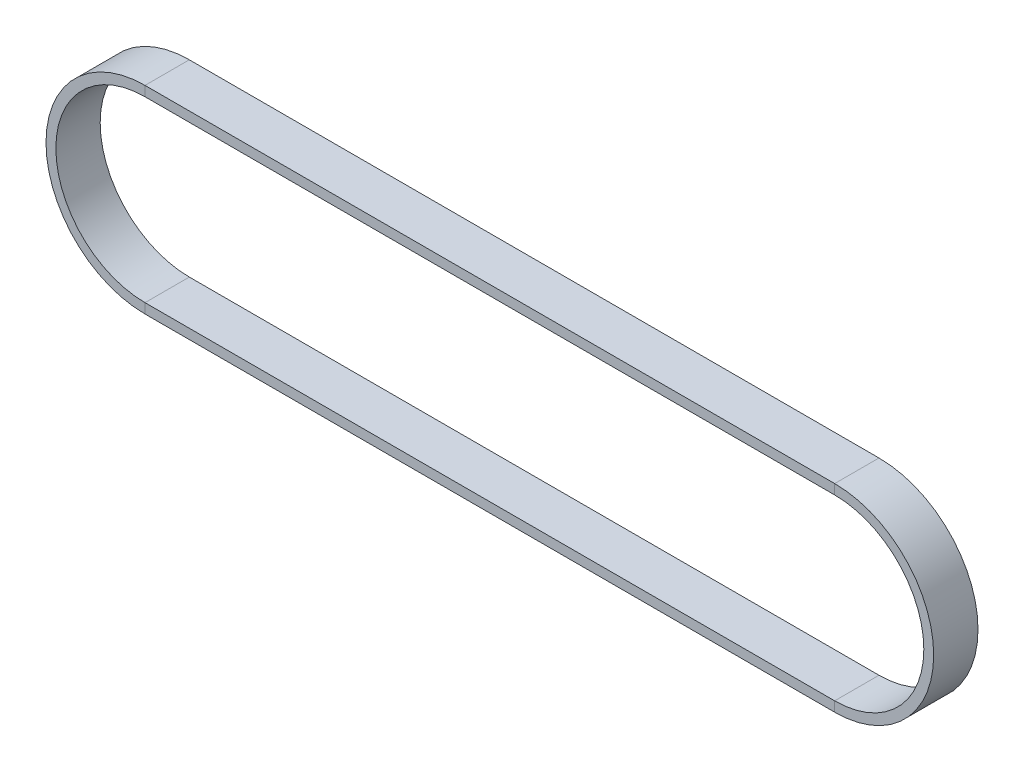
SolidWorks part; units mm, degrees
ref_plane "Front Plane" through (0, 0, 0) normal (0, 0, 1) x (1, 0, 0)
ref_plane "Top Plane" through (0, 0, 0) normal (0, 1, 0) x (1, 0, 0)
ref_plane "Right Plane" through (0, 0, 0) normal (1, 0, 0) x (0, 0, -1)
sketch "Sketch1" plane through (0, 0, 0) normal (0, 0, 1) x (1, 0, 0)
  line L0 (0, 19.1008) -> (140.0251, 19.1008)
  line L1 (0, -19.1008) -> (140.0251, -19.1008)
  arc A0 (0, 19.1008) -> (0, -19.1008) centre (0, 0) ccw
  arc A1 (140.0251, -19.1008) -> (140.0251, 19.1008) centre (140.0251, 0) ccw
  dimension "D1" = 38.2016
  dimension "D2" = 38.2016
  dimension "D3" = 140.0251
sketch "Sketch2" plane through (0, 0, 0) normal (1, 0, 0) x (0, 0, -1)
  line L1 (4.5, 18.1008) -> (-4.5, 18.1008)
  line L2 (4.5, 18.1008) -> (4.5, 20.1008)
  line L3 (4.5, 20.1008) -> (-4.5, 20.1008)
  line L4 (-4.5, 18.1008) -> (-4.5, 20.1008)
  line L5 (4.5, 18.1008) -> (-4.5, 20.1008) construction
  line L6 (4.5, 20.1008) -> (-4.5, 18.1008) construction
  point P0 (0, 19.1008)
  point P2 (0, 19.1008)
  dimension "D1" = 2
  dimension "D2" = 9
sweep "Sweep1" add profiles "Sketch2" path "Sketch1"
